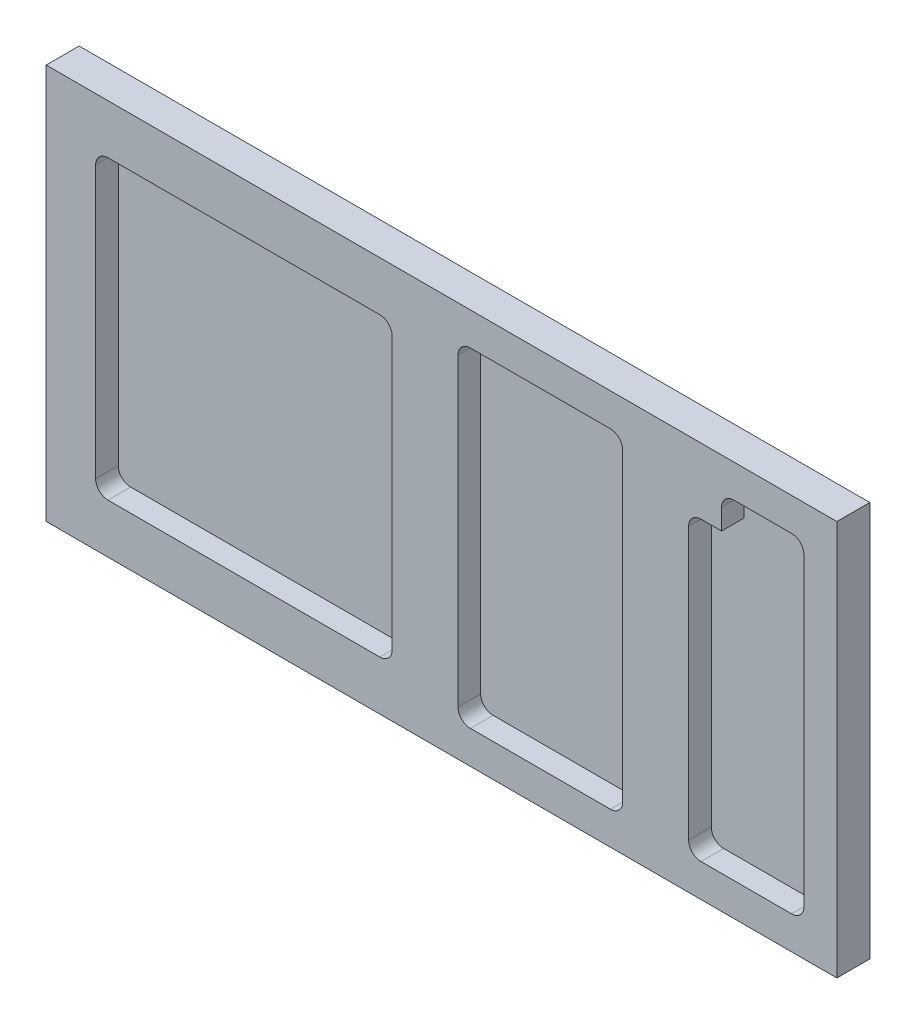
SolidWorks part; units mm, degrees
ref_plane "Front Plane" through (0, 0, 0) normal (0, 0, 1) x (1, 0, 0)
ref_plane "Top Plane" through (0, 0, 0) normal (0, 1, 0) x (1, 0, 0)
ref_plane "Right Plane" through (0, 0, 0) normal (1, 0, 0) x (0, 0, -1)
sketch "Sketch1" plane through (0, 0, 0) normal (0, 0, 1) x (1, 0, 0)
  line L1 (-152.4, 76.2) -> (152.4, 76.2)
  line L2 (-152.4, 76.2) -> (-152.4, -76.2)
  line L3 (-152.4, -76.2) -> (152.4, -76.2)
  line L4 (152.4, 76.2) -> (152.4, -76.2)
  line L5 (-152.4, 76.2) -> (152.4, -76.2) construction
  line L6 (-152.4, -76.2) -> (152.4, 76.2) construction
  point P0 (0, 0)
  dimension "D1" = 304.8
  dimension "D2" = 152.4
extrude "Boss-Extrude1" add sketch "Sketch1" along normal blind 12.7
sketch "Sketch2" plane through (0, 0, 12.7) normal (0, 0, 1) x (1, 0, 0)
  line L0 (152.4, 76.2) -> (-152.4, 76.2) construction
  line L1 (-128.5875, 57.15) -> (-23.8125, 57.15)
  line L2 (-133.35, 52.3875) -> (-133.35, -52.3875)
  line L3 (-128.5875, -57.15) -> (-23.8125, -57.15)
  line L4 (-19.05, 52.3875) -> (-19.05, -52.3875)
  line L5 (-133.35, 57.15) -> (-19.05, -57.15) construction
  line L6 (-133.35, -57.15) -> (-19.05, 57.15) construction
  line L7 (-152.4, 76.2) -> (-152.4, -76.2) construction
  line L8 (-152.4, -76.2) -> (152.4, -76.2) construction
  arc A0 (-133.35, -52.3875) -> (-128.5875, -57.15) centre (-128.5875, -52.3875) ccw
  arc A1 (-23.8125, -57.15) -> (-19.05, -52.3875) centre (-23.8125, -52.3875) ccw
  arc A2 (-23.8125, 57.15) -> (-19.05, 52.3875) centre (-23.8125, 52.3875) cw
  arc A3 (-128.5875, 57.15) -> (-133.35, 52.3875) centre (-128.5875, 52.3875) ccw
  point P0 (-76.2, 0)
  dimension "D5" = 4.7625
  dimension "D1" = 19.05
  dimension "D2" = 19.05
  dimension "D3" = 19.05
  dimension "D4" = 114.3
extrude "Cut-Extrude1" cut sketch "Sketch2" against normal blind 8.7325
sketch "Sketch3" plane through (0, 0, 12.7) normal (0, 0, 1) x (1, 0, 0)
  line L0 (152.4, 76.2) -> (-152.4, 76.2) construction
  line L1 (100.0125, 50.8) -> (107.95, 50.8)
  line L2 (95.25, 46.0375) -> (95.25, -58.7375)
  line L3 (100.0125, -63.5) -> (134.9375, -63.5)
  line L4 (139.7, 50.8) -> (139.7, -58.7375)
  line L5 (95.25, 50.8) -> (139.7, -63.5) construction
  line L6 (95.25, -63.5) -> (139.7, 50.8) construction
  line L7 (-152.4, -76.2) -> (152.4, -76.2) construction
  line L8 (152.4, -76.2) -> (152.4, 76.2) construction
  line L10 (11.1125, 63.5) -> (65.0875, 63.5)
  line L11 (6.35, 58.7375) -> (6.35, -58.7375)
  line L12 (11.1125, -63.5) -> (65.0875, -63.5)
  line L13 (69.85, 58.7375) -> (69.85, -58.7375)
  line L14 (6.35, 63.5) -> (69.85, -63.5) construction
  line L15 (6.35, -63.5) -> (69.85, 63.5) construction
  line L17 (139.7, 50.8) -> (139.7, 58.7375)
  line L18 (134.9375, 63.5) -> (112.7125, 63.5)
  line L19 (107.95, 50.8) -> (107.95, 58.7375)
  arc A0 (100.0125, 50.8) -> (95.25, 46.0375) centre (100.0125, 46.0375) ccw
  arc A1 (112.7125, 63.5) -> (107.95, 58.7375) centre (112.7125, 58.7375) ccw
  arc A2 (139.7, 58.7375) -> (134.9375, 63.5) centre (134.9375, 58.7375) ccw
  arc A3 (134.9375, -63.5) -> (139.7, -58.7375) centre (134.9375, -58.7375) ccw
  arc A4 (95.25, -58.7375) -> (100.0125, -63.5) centre (100.0125, -58.7375) ccw
  arc A5 (6.35, -58.7375) -> (11.1125, -63.5) centre (11.1125, -58.7375) ccw
  arc A6 (65.0875, -63.5) -> (69.85, -58.7375) centre (65.0875, -58.7375) ccw
  arc A7 (65.0875, 63.5) -> (69.85, 58.7375) centre (65.0875, 58.7375) cw
  arc A8 (11.1125, 63.5) -> (6.35, 58.7375) centre (11.1125, 58.7375) ccw
  point P0 (117.475, -6.35)
  point P11 (38.1, 0)
  dimension "D11" = 4.7625
  dimension "D1" = 25.4
  dimension "D2" = 12.7
  dimension "D3" = 12.7
  dimension "D4" = 44.45
  dimension "D5" = 63.5
  dimension "D6" = 82.55
  dimension "D7" = 12.7
  dimension "D8" = 12.7
  dimension "D9" = 12.7
  dimension "D10" = 44.45
extrude "Cut-Extrude2" cut sketch "Sketch3" against normal blind 8.7325
